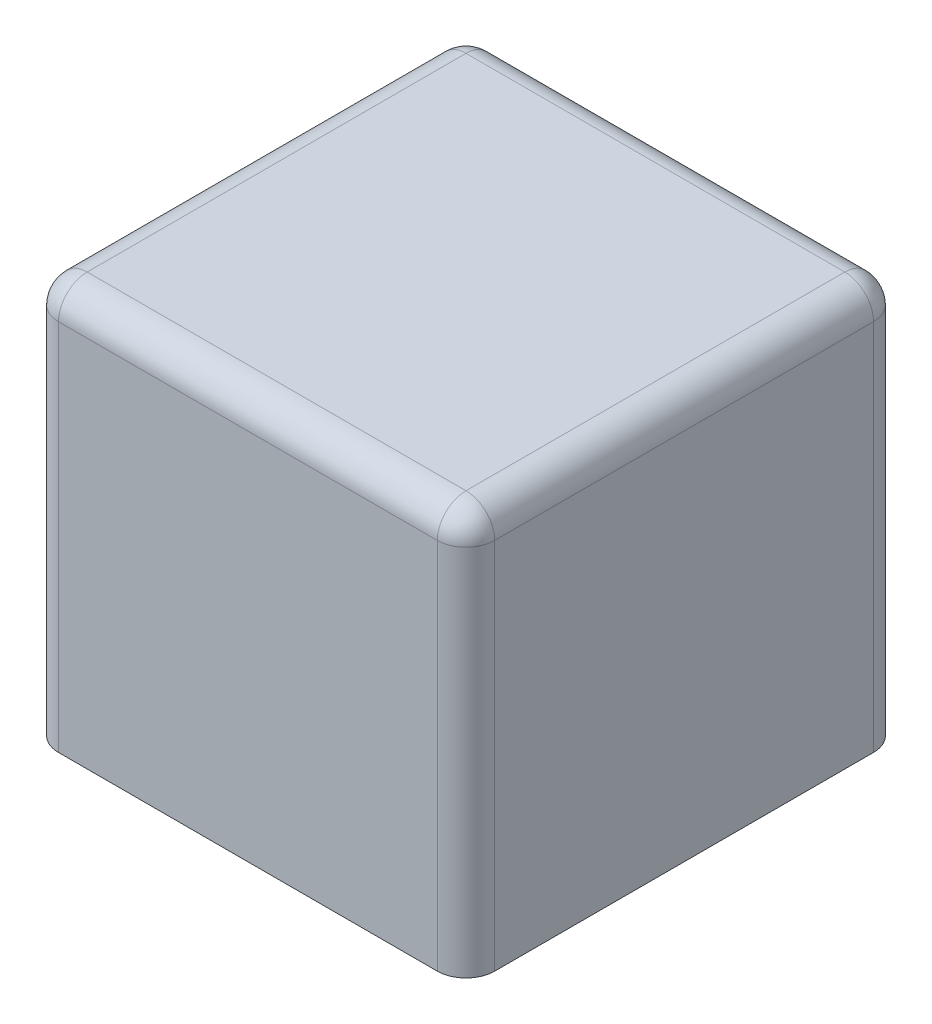
SolidWorks part; units mm, degrees
ref_plane "Front Plane" through (0, 0, 0) normal (0, 0, 1) x (1, 0, 0)
ref_plane "Top Plane" through (0, 0, 0) normal (0, 1, 0) x (1, 0, 0)
ref_plane "Right Plane" through (0, 0, 0) normal (1, 0, 0) x (0, 0, -1)
sketch "Sketch1" plane through (0, 0, 0) normal (0, 1, 0) x (1, 0, 0)
  line L1 (-3.8, 3.8) -> (3.8, 3.8)
  line L2 (-3.8, 3.8) -> (-3.8, -3.8)
  line L3 (-3.8, -3.8) -> (3.8, -3.8)
  line L4 (3.8, 3.8) -> (3.8, -3.8)
  line L5 (-3.8, 3.8) -> (3.8, -3.8) construction
  line L6 (-3.8, -3.8) -> (3.8, 3.8) construction
  point P0 (0, 0)
  dimension "D1" = 7.6
  dimension "D2" = 7.6
extrude "Boss-Extrude1" add sketch "Sketch1" along normal blind 7
sketch "Sketch2" plane through (0, 0, 0) normal (0, -1, 0) x (1, 0, 0)
  line L8 (-3.3, 3.3) -> (-3.3, -3.3)
  line L9 (-3.3, -3.3) -> (3.3, -3.3)
  line L10 (3.3, -3.3) -> (3.3, 3.3)
  line L11 (3.3, 3.3) -> (-3.3, 3.3)
  line L12 (-3.3, 3.3) -> (-3.3, -3.3)
  line L13 (-3.3, -3.3) -> (3.3, -3.3)
  line L14 (3.3, -3.3) -> (3.3, 3.3)
  line L15 (3.3, 3.3) -> (-3.3, 3.3)
  dimension "D1" = 0.5
extrude "Cut-Extrude1" cut sketch "Sketch2" against normal blind 6.5
fillet "Fillet2" radius 0.5 16 edges at (3.3, 3.25, -3.3) (3.3, 6.5, 0) (3.3, 3.25, 3.3) (0, 6.5, 3.3) (-3.3, 3.25, 3.3) (-3.3, 6.5, 0) (0, 6.5, -3.3) (-3.3, 3.25, -3.3) (0, 7, -3.8) (3.8, 7, 0) (3.8, 3.5, 3.8) (0, 7, 3.8) (-3.8, 7, 0) (-3.8, 3.5, 3.8) (-3.8, 3.5, -3.8) (3.8, 3.5, -3.8)
equation "\"D1@Sketch1\"=\"D2@Sketch1\""
